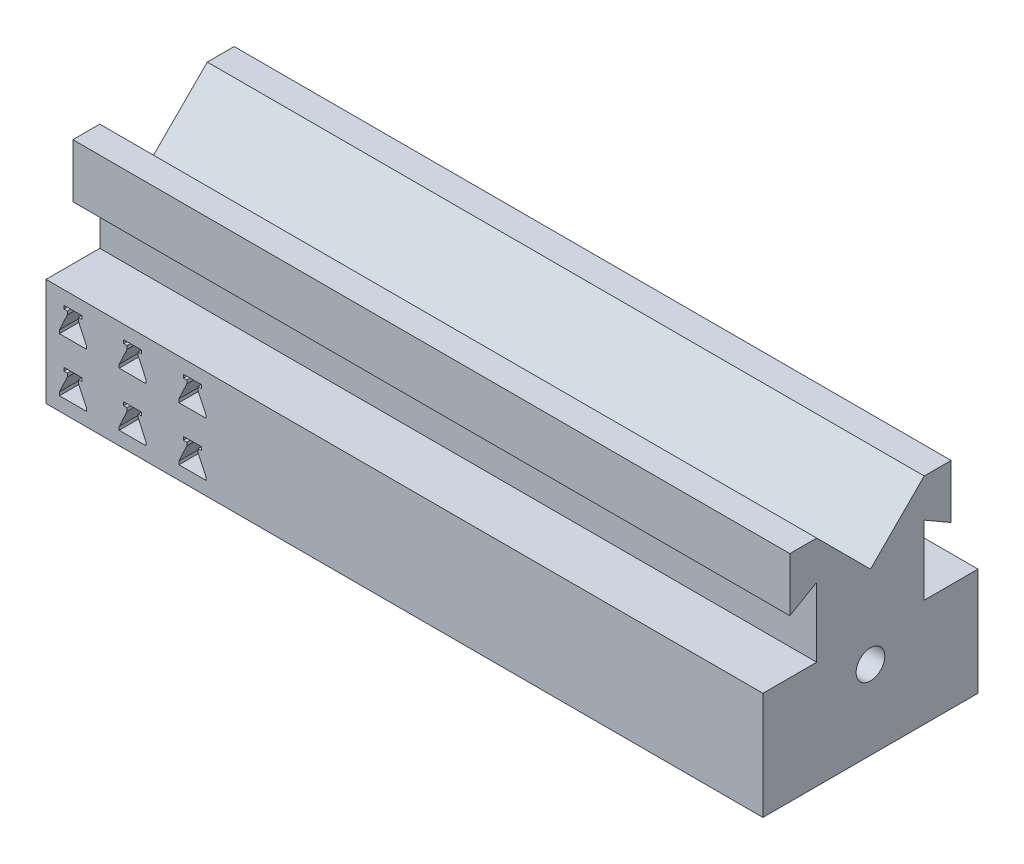
SolidWorks part; units mm, degrees
ref_plane "Front Plane" through (0, 0, 0) normal (0, 0, 1) x (1, 0, 0)
ref_plane "Top Plane" through (0, 0, 0) normal (0, 1, 0) x (1, 0, 0)
ref_plane "Right Plane" through (0, 0, 0) normal (1, 0, 0) x (0, 0, -1)
sketch "Base" plane through (0, 0, 0) normal (0, 1, 0) x (1, 0, 0)
  line L0 (0, 0) -> (63.5, 0)
  line L1 (-41.5655, 0) -> (41.5655, 0) construction
  line L2 (63.5, 0) -> (122.1126, 0)
  line L4 (0, -41.5655) -> (0, 41.5655) construction
  line L6 (127, -38.1) -> (127, 0)
  line L7 (127, 0) -> (122.1126, 0)
  line L8 (122.1126, 0) -> (0, 0) construction
  line L9 (0, 0) -> (0, -38.1) construction
  line L10 (0, -38.1) -> (127, -38.1) construction
  line L11 (127, -38.1) -> (31.75, -38.1)
  line L12 (31.75, -38.1) -> (0, -38.1)
  line L14 (0, 0) -> (0, -38.1)
  line L15 (122.1126, 0) -> (0, 0) construction
  dimension "D2" = 127
  dimension "D3" = 38.1
  dimension "D4" = 63.5
  dimension "D5" = 0
  dimension "D1" = 0
  dimension "D6" = 31.75
ref_plane "Plane1" through (127, 0, 0) normal (1, 0, 0) x (0, 0, -1)
extrude "Boss-Extrude2" add sketch "Base" along normal blind 19.05
sketch "Sketch3" plane through (127, 0, 0) normal (1, 0, 0) x (0, 0, -1)
  line L0 (0, 0) -> (-38.1, 0) construction
  line L1 (-38.1, 0) -> (0, 0) construction
  line L2 (-38.1, 0) -> (-38.1, 38.1) construction
  line L3 (-38.1, 38.1) -> (0, 38.1) construction
  line L4 (0, 0) -> (0, 38.1) construction
  line L5 (-38.1, 38.1) -> (-28.575, 38.1)
  line L6 (-28.575, 38.1) -> (-19.05, 28.575)
  line L7 (-19.05, 28.575) -> (-9.525, 38.1)
  line L8 (-9.525, 38.1) -> (0, 38.1)
  line L9 (0, 38.1) -> (0, 0)
  line L10 (0, 0) -> (-38.1, 0)
  line L11 (-38.1, 0) -> (-38.1, 38.1)
  dimension "D1" = 19.05
extrude "Boss-Extrude1" add sketch "Sketch3" against normal up to surface (127 mm away) up to plane "Right Plane"
sketch "Sketch5" plane through (0, 0, 0) normal (0, 0, 1) x (1, 0, 0)
  line L1 (-25.8204, 0) -> (214.209, 0)
  line L2 (-25.8204, 0) -> (-25.8204, 75.5736)
  line L3 (-25.8204, 75.5736) -> (214.209, 75.5736)
  line L4 (214.209, 0) -> (214.209, 75.5736)
sketch "Sketch6" plane through (127, 0, 0) normal (1, 0, 0) x (0, 0, -1)
  line L0 (-19.05, 13.97) -> (-19.05, 28.575) construction
  line L1 (-28.575, 38.1) -> (-38.1, 38.1) construction
  circle A0 centre (-19.05, 13.97) radius 2.54
  dimension "D1" = 5.08
  dimension "D2" = 24.13
extrude "Cut-Extrude2" cut sketch "Sketch6" against normal through all
sketch "Sketch7" plane through (0, 0, 0) normal (0, 1, 0) x (1, 0, 0)
  line L1 (0, 0) -> (200, 0)
  line L2 (0, 0) -> (0, -200)
  line L3 (0, -200) -> (200, -200)
  line L4 (200, 0) -> (200, -200)
  dimension "D1" = 200
  dimension "D2" = 200
sketch "Sketch8" plane through (127, 0, 0) normal (1, 0, 0) x (0, 0, -1)
  line L2 (-4.7625, 28.575) -> (-4.7625, 38.1)
  line L3 (-4.7625, 38.1) -> (0, 38.1)
  line L4 (0, 19.05) -> (0, 38.1)
  line L8 (-9.525, 31.3246) -> (-9.525, 19.05)
  line L9 (-9.525, 31.3246) -> (-4.7625, 28.575)
  line L10 (-9.525, 19.05) -> (0, 19.05)
  line L11 (-19.05, 28.575) -> (-19.05, 0) construction
  line L12 (0, 0) -> (-200, 0) construction
  line L13 (-28.575, 19.05) -> (-38.1, 19.05)
  line L14 (-28.575, 31.3246) -> (-33.3375, 28.575)
  line L15 (-28.575, 31.3246) -> (-28.575, 19.05)
  line L16 (-38.1, 19.05) -> (-38.1, 38.1)
  line L17 (-33.3375, 38.1) -> (-38.1, 38.1)
  line L18 (-33.3375, 28.575) -> (-33.3375, 38.1)
  dimension "D1" = 4.7625
  dimension "D2" = 60
  dimension "D3" = 9.525
  dimension "D4" = 19.05
  dimension "D5" = 9.525
extrude "Cut-Extrude3" cut sketch "Sketch8" against normal through all
sketch "Sketch9" plane through (0, 0, 38.1) normal (0, 0, 1) x (1, 0, 0)
  line L0 (0, 19.05) -> (127, 19.05) construction
  line L7 (3.175, 16.6688) -> (6.35, 16.6688)
  line L12 (6.35, 16.6688) -> (6.35, 16.0734)
  line L13 (6.35, 16.0734) -> (5.7547, 16.0734)
  line L14 (5.7547, 16.0734) -> (5.7547, 15.4781)
  line L15 (5.7547, 15.4781) -> (7.1437, 12.5016)
  line L16 (7.1437, 12.5016) -> (7.1437, 11.9063)
  line L17 (7.1437, 11.9063) -> (2.3812, 11.9063)
  line L18 (4.7625, 16.6688) -> (4.7625, 11.9063) construction
  line L19 (2.3812, 12.5016) -> (2.3812, 11.9063)
  line L20 (3.7703, 15.4781) -> (2.3812, 12.5016)
  line L21 (3.7703, 16.0734) -> (3.7703, 15.4781)
  line L22 (3.175, 16.0734) -> (3.7703, 16.0734)
  line L23 (3.175, 16.6688) -> (3.175, 16.0734)
  line L24 (0, -41.5655) -> (0, 41.5655) construction
  dimension "D1" = 1.5875
  dimension "D2" = 4.7625
  dimension "D3" = 2.3813
  dimension "D4" = 0.5953
  dimension "D5" = 2.3813
  dimension "D6" = 2.3813
extrude "Cut-Extrude4" cut sketch "Sketch9" against normal through all
pattern_linear "LPattern1" count 3 spacing 10.5833 along (1, 0, 0) count 2 spacing 9.525 along (0, -1, 0) of "Cut-Extrude4"
equation "\"ViseLength\"= 5in'length of vise in inches"
equation "\"Angle\"= 0'Angle of vise in degrees"
equation "\"ViseWidth\"= 1.5in'width of vise (approximately the scaling factor)"
equation "\"D2@Base\" = \"ViseLength\""
equation "\"D3@Base\" = \"ViseWidth\""
equation "\"D4@Base\" = \"ViseLength\" / 2"
equation "\"D5@Base\" = \"Angle\""
equation "\"D1@Sketch3\"=\"ViseWidth\"/2"
equation "\"D1@Boss-Extrude2\"=\"ViseWidth\"/2"
equation "\"D1@Base\"=\"Angle\""
equation "\"D6@Base\"=\"ViseLength\"/4"
equation "\"D2@Sketch6\"=\"ViseWidth\"/2+.2"
equation "\"D1@Sketch8\"=\"ViseWidth\"/8"
equation "\"D3@Sketch8\"=\"ViseWidth\"/4"
equation "\"D4@Sketch8\"=\"ViseWidth\"/2"
equation "\"D5@Sketch8\"=\"ViseWidth\"/4"
equation "\"flask\"= \"ViseWidth\" / 8"
equation "\"D1@Sketch9\"=\"flask\"/3"
equation "\"D2@Sketch9\"=\"flask\""
equation "\"D3@Sketch9\"=\"flask\"/2"
equation "\"D4@Sketch9\"=\"flask\"/8"
equation "\"D5@Sketch9\"=\"ViseWidth\"/16"
equation "\"D6@Sketch9\"=\"ViseWidth\"/16"
equation "\"D3@LPattern1\"=\"ViseLength\"/12"
equation "\"D4@LPattern1\"=\"ViseWidth\"/4"
